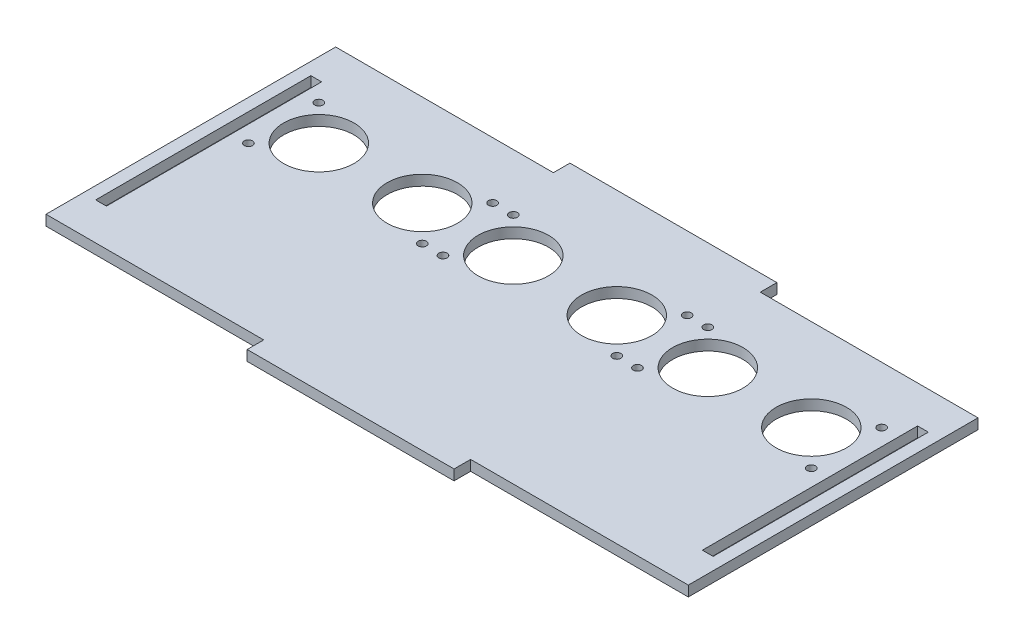
SolidWorks part; units mm, degrees
ref_plane "Front Plane" through (0, 0, 0) normal (0, 0, 1) x (1, 0, 0)
ref_plane "Top Plane" through (0, 0, 0) normal (0, 1, 0) x (1, 0, 0)
ref_plane "Right Plane" through (0, 0, 0) normal (1, 0, 0) x (0, 0, -1)
sketch "Sketch1" plane through (0, 0, 0) normal (0, 1, 0) x (1, 0, 0)
  line L0 (-25, 35) -> (-77.6, 35)
  line L1 (-77.6, 35) -> (-77.6, -35)
  line L2 (-77.6, -35) -> (-25, -35)
  line L3 (-25, -35) -> (-25, -39)
  line L4 (-25, -39) -> (25, -39)
  line L5 (-74.6, 26) -> (-72, 26)
  line L6 (-72, -26) -> (-72, 26)
  line L7 (-74.6, -26) -> (-72, -26)
  line L8 (-74.6, -26) -> (-74.6, 26)
  line L9 (0, -112.7216) -> (0, 112.7216) construction
  line L10 (112.7216, 0) -> (-112.7216, 0) construction
  line L11 (25, 35) -> (77.6, 35)
  line L12 (74.6, -26) -> (74.6, 26)
  line L13 (74.6, -26) -> (72, -26)
  line L14 (72, -26) -> (72, 26)
  line L15 (74.6, 26) -> (72, 26)
  line L16 (77.6, 35) -> (77.6, -35)
  line L17 (77.6, -35) -> (25, -35)
  line L18 (25, -35) -> (25, -39)
  line L19 (25, 35) -> (25, 39)
  line L20 (-25, 35) -> (-25, 39)
  line L21 (-25, 39) -> (25, 39)
  line L22 (-28.5048, 12.8182) -> (28.5048, 12.8182) construction
  line L23 (0, -1.7183) -> (0, 27.3547) construction
  circle A0 centre (-12.5, 12.8182) radius 8.5
  circle A1 centre (-21, 21.3182) radius 1
  circle A2 centre (-21, 4.3182) radius 1
  circle A3 centre (21, 4.3182) radius 1
  circle A4 centre (21, 21.3182) radius 1
  circle A5 centre (12.5, 12.8182) radius 8.5
  circle A8 centre (26, 4.3182) radius 1
  circle A9 centre (34.5, 12.8182) radius 8.5
  circle A10 centre (26, 21.3182) radius 1
  circle A11 centre (68, 21.3182) radius 1
  circle A12 centre (68, 4.3182) radius 1
  circle A13 centre (59.5, 12.8182) radius 8.5
  circle A14 centre (-68, 4.3182) radius 1
  circle A15 centre (-59.5, 12.8182) radius 8.5
  circle A16 centre (-34.5, 12.8182) radius 8.5
  circle A17 centre (-26, 21.3182) radius 1
  circle A18 centre (-26, 4.3182) radius 1
  circle A19 centre (-68, 21.3182) radius 1
  point P0 (42.5, 12.8182)
  point P1 (-77.6, 0)
  point P20 (0, 0)
  point P23 (0, 0)
  point P29 (0, 113.7691)
  point P43 (0, 12.8182)
  point P45 (0, 12.8182)
  dimension "D10" = 17
  dimension "D11" = 2
  dimension "D1" = 4
  dimension "D2" = 25
  dimension "D3" = 2.6
  dimension "D4" = 2.6
  dimension "D5" = 3
  dimension "D6" = 70
  dimension "D7" = 35
  dimension "D8" = 52
  dimension "D9" = 26
  dimension "D12" = 17
  dimension "D13" = 25
  dimension "D14" = 8.5
  dimension "D17" = 0
extrude "Boss-Extrude1" add sketch "Sketch1" along normal blind 2.5
